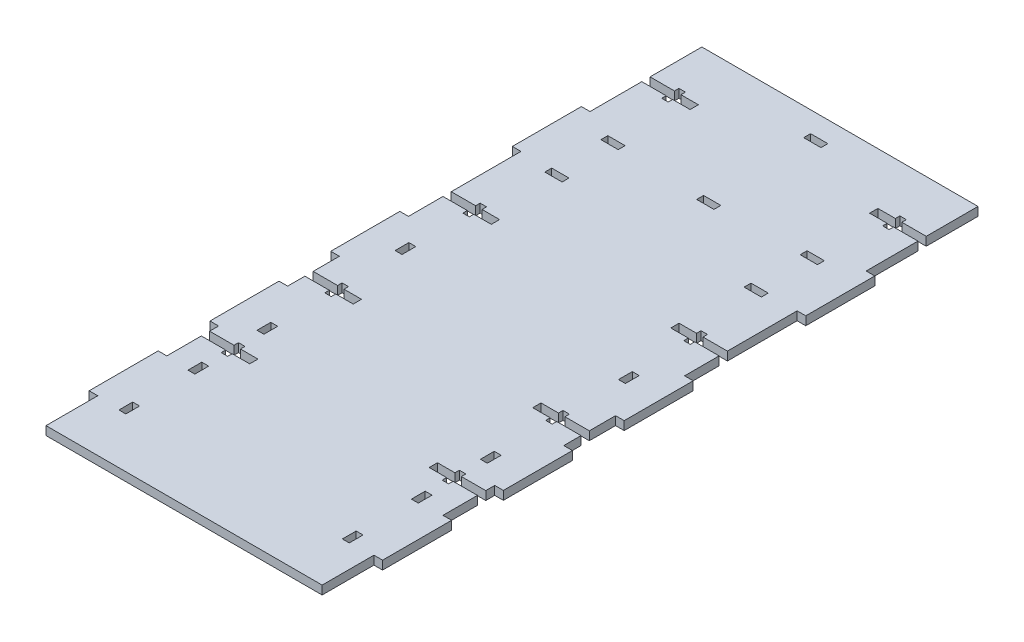
SolidWorks part; units mm, degrees
ref_plane "Front Plane" through (0, 0, 0) normal (0, 0, 1) x (1, 0, 0)
ref_plane "Top Plane" through (0, 0, 0) normal (0, 1, 0) x (1, 0, 0)
ref_plane "Right Plane" through (0, 0, 0) normal (1, 0, 0) x (0, 0, -1)
sketch "Sketch1" plane through (0, 0, 0) normal (0, 1, 0) x (1, 0, 0)
  line L1 (0, 0) -> (101.6, 0)
  line L2 (0, 0) -> (0, 241.3)
  line L3 (0, 241.3) -> (101.6, 241.3)
  line L4 (101.6, 0) -> (101.6, 241.3)
  dimension "D1" = 101.6
  dimension "D2" = 241.3
extrude "Boss-Extrude1" add sketch "Sketch1" along normal blind 3.175
sketch "Sketch2" plane through (0, 3.175, 0) normal (0, 1, 0) x (1, 0, 0)
  line L0 (50.8, 241.3) -> (50.8, 0) construction
  line L1 (8.4285, 23.4802) -> (10.9685, 23.4802)
  line L2 (8.4285, 23.4802) -> (8.4285, 18.4002)
  line L3 (8.4285, 18.4002) -> (10.9685, 18.4002)
  line L4 (10.9685, 23.4802) -> (10.9685, 18.4002)
  line L5 (101.6, 241.3) -> (0, 241.3) construction
  line L6 (0, 0) -> (101.6, 0) construction
  line L7 (8.4285, 48.8802) -> (8.4285, 43.8002)
  line L8 (19.05, 88.9) -> (82.55, 88.9)
  line L9 (19.05, 88.9) -> (19.05, 0)
  line L10 (19.05, 0) -> (82.55, 0)
  line L11 (82.55, 88.9) -> (82.55, 0)
  line L12 (19.05, 88.9) -> (82.55, 0) construction
  line L13 (19.05, 0) -> (82.55, 88.9) construction
  line L14 (8.4285, 48.8802) -> (10.9685, 48.8802)
  line L15 (10.9685, 48.8802) -> (10.9685, 43.8002)
  line L16 (8.4285, 43.8002) -> (10.9685, 43.8002)
  line L17 (8.4285, 74.2802) -> (8.4285, 69.2002)
  line L18 (8.4285, 74.2802) -> (10.9685, 74.2802)
  line L19 (10.9685, 74.2802) -> (10.9685, 69.2002)
  line L20 (8.4285, 69.2002) -> (10.9685, 69.2002)
  line L21 (0, 177.8) -> (0, 190.5)
  line L22 (19.05, 165.1) -> (82.55, 165.1)
  line L23 (19.05, 165.1) -> (19.05, 101.6)
  line L24 (19.05, 101.6) -> (82.55, 101.6)
  line L25 (82.55, 165.1) -> (82.55, 101.6)
  line L26 (19.05, 165.1) -> (82.55, 101.6) construction
  line L27 (19.05, 101.6) -> (82.55, 165.1) construction
  line L28 (0, 177.8) -> (28.575, 177.8)
  line L29 (0, 190.5) -> (28.575, 190.5)
  line L30 (28.575, 177.8) -> (28.575, 190.5)
  line L31 (0, 241.3) -> (0, 0) construction
  line L32 (8.4285, 125.0802) -> (8.4285, 120.0002)
  line L33 (22.225, 228.6) -> (79.375, 228.6)
  line L34 (22.225, 228.6) -> (22.225, 196.85)
  line L35 (22.225, 196.85) -> (79.375, 196.85)
  line L36 (79.375, 228.6) -> (79.375, 196.85)
  line L37 (22.225, 228.6) -> (79.375, 196.85) construction
  line L38 (22.225, 196.85) -> (79.375, 228.6) construction
  line L39 (8.4285, 125.0802) -> (10.9685, 125.0802)
  line L40 (10.9685, 125.0802) -> (10.9685, 120.0002)
  line L41 (8.4285, 120.0002) -> (10.9685, 120.0002)
  line L42 (0, 184.15) -> (28.575, 184.15) construction
  line L43 (10.9685, 175.0986) -> (17.3185, 175.0986)
  line L44 (10.9685, 175.0986) -> (10.9685, 172.5586)
  line L45 (10.9685, 172.5586) -> (17.3185, 172.5586)
  line L46 (17.3185, 175.0986) -> (17.3185, 172.5586)
  line L47 (10.9685, 195.7414) -> (17.3185, 195.7414)
  line L48 (17.3185, 193.2014) -> (17.3185, 195.7414)
  line L49 (10.9685, 193.2014) -> (17.3185, 193.2014)
  line L50 (10.9685, 193.2014) -> (10.9685, 195.7414)
  line L51 (22.225, 212.725) -> (79.375, 212.725) construction
  line L52 (47.625, 194.31) -> (53.975, 194.31)
  line L53 (47.625, 194.31) -> (47.625, 191.77)
  line L54 (47.625, 191.77) -> (53.975, 191.77)
  line L55 (53.975, 194.31) -> (53.975, 191.77)
  line L56 (47.625, 194.31) -> (53.975, 191.77) construction
  line L57 (47.625, 191.77) -> (53.975, 194.31) construction
  line L58 (47.625, 233.68) -> (53.975, 233.68)
  line L59 (53.975, 231.14) -> (53.975, 233.68)
  line L60 (47.625, 231.14) -> (53.975, 231.14)
  line L61 (47.625, 231.14) -> (47.625, 233.68)
  line L62 (17.78, 220.726) -> (0, 220.726) construction
  line L63 (0, 60.198) -> (8.9694, 60.198)
  line L64 (0, 60.198) -> (0, 57.15)
  line L65 (0, 57.15) -> (8.9694, 57.15)
  line L66 (17.78, 60.198) -> (17.78, 57.15)
  line L71 (0, 98.298) -> (8.9694, 98.298)
  line L72 (0, 98.298) -> (0, 95.25)
  line L73 (0, 95.25) -> (8.9694, 95.25)
  line L74 (17.78, 98.298) -> (17.78, 95.25)
  line L75 (0, 149.098) -> (8.9694, 149.098)
  line L76 (0, 149.098) -> (0, 146.05)
  line L77 (0, 146.05) -> (8.9694, 146.05)
  line L78 (17.78, 149.098) -> (17.78, 146.05)
  line L79 (0, 222.25) -> (8.9694, 222.25)
  line L80 (0, 222.25) -> (0, 219.202)
  line L81 (0, 219.202) -> (8.9694, 219.202)
  line L82 (17.78, 222.25) -> (17.78, 219.202)
  line L83 (8.9694, 217.551) -> (11.3506, 217.551)
  line L84 (8.9694, 217.551) -> (8.9694, 219.202)
  line L85 (8.9694, 223.901) -> (11.3506, 223.901)
  line L86 (11.3506, 217.551) -> (11.3506, 219.202)
  line L87 (8.9694, 217.551) -> (11.3506, 223.901) construction
  line L88 (8.9694, 223.901) -> (11.3506, 217.551) construction
  line L89 (8.9694, 222.25) -> (8.9694, 223.901)
  line L90 (11.3506, 222.25) -> (11.3506, 223.901)
  line L91 (9.5885, 222.25) -> (10.7315, 222.25)
  line L92 (11.3506, 222.25) -> (17.78, 222.25)
  line L93 (11.3506, 219.202) -> (17.78, 219.202)
  line L94 (0, 147.574) -> (17.78, 147.574) construction
  line L95 (0, 96.774) -> (17.78, 96.774) construction
  line L96 (8.9694, 144.399) -> (11.3506, 144.399)
  line L97 (8.9694, 144.399) -> (8.9694, 146.05)
  line L98 (8.9694, 150.749) -> (11.3506, 150.749)
  line L99 (11.3506, 144.399) -> (11.3506, 146.05)
  line L100 (8.9694, 144.399) -> (11.3506, 150.749) construction
  line L101 (8.9694, 150.749) -> (11.3506, 144.399) construction
  line L102 (0, 58.674) -> (17.78, 58.674) construction
  line L103 (8.9694, 93.599) -> (11.3506, 93.599)
  line L104 (8.9694, 93.599) -> (8.9694, 95.25)
  line L105 (8.9694, 99.949) -> (11.3506, 99.949)
  line L106 (11.3506, 93.599) -> (11.3506, 95.25)
  line L107 (8.9694, 93.599) -> (11.3506, 99.949) construction
  line L108 (8.9694, 99.949) -> (11.3506, 93.599) construction
  line L109 (11.3506, 98.298) -> (17.78, 98.298)
  line L110 (8.9694, 55.499) -> (11.3506, 55.499)
  line L111 (8.9694, 55.499) -> (8.9694, 57.15)
  line L112 (8.9694, 61.849) -> (11.3506, 61.849)
  line L113 (11.3506, 55.499) -> (11.3506, 57.15)
  line L114 (8.9694, 55.499) -> (11.3506, 61.849) construction
  line L115 (8.9694, 61.849) -> (11.3506, 55.499) construction
  line L116 (8.9694, 98.298) -> (8.9694, 99.949)
  line L117 (11.3506, 95.25) -> (17.78, 95.25)
  line L118 (11.3506, 98.298) -> (11.3506, 99.949)
  line L119 (11.3506, 57.15) -> (17.78, 57.15)
  line L120 (11.3506, 60.198) -> (11.3506, 61.849)
  line L121 (11.3506, 60.198) -> (17.78, 60.198)
  line L122 (8.9694, 60.198) -> (8.9694, 61.849)
  line L123 (8.9694, 149.098) -> (8.9694, 150.749)
  line L124 (11.3506, 149.098) -> (17.78, 149.098)
  line L125 (11.3506, 149.098) -> (11.3506, 150.749)
  line L126 (11.3506, 146.05) -> (17.78, 146.05)
  line L127 (93.1715, 18.4002) -> (90.6315, 18.4002)
  line L128 (90.6315, 23.4802) -> (90.6315, 18.4002)
  line L129 (93.1715, 23.4802) -> (90.6315, 23.4802)
  line L130 (93.1715, 23.4802) -> (93.1715, 18.4002)
  line L131 (90.2494, 60.198) -> (90.2494, 61.849)
  line L132 (92.6306, 61.849) -> (90.2494, 61.849)
  line L133 (92.6306, 60.198) -> (92.6306, 61.849)
  line L134 (101.6, 60.198) -> (92.6306, 60.198)
  line L135 (101.6, 60.198) -> (101.6, 57.15)
  line L136 (101.6, 57.15) -> (92.6306, 57.15)
  line L137 (92.6306, 55.499) -> (92.6306, 57.15)
  line L138 (92.6306, 55.499) -> (90.2494, 55.499)
  line L139 (90.2494, 55.499) -> (90.2494, 57.15)
  line L140 (90.2494, 57.15) -> (83.82, 57.15)
  line L141 (83.82, 60.198) -> (83.82, 57.15)
  line L142 (90.2494, 60.198) -> (83.82, 60.198)
  line L143 (93.1715, 48.8802) -> (90.6315, 48.8802)
  line L144 (90.6315, 48.8802) -> (90.6315, 43.8002)
  line L145 (93.1715, 43.8002) -> (90.6315, 43.8002)
  line L146 (93.1715, 48.8802) -> (93.1715, 43.8002)
  line L147 (93.1715, 74.2802) -> (90.6315, 74.2802)
  line L148 (90.6315, 74.2802) -> (90.6315, 69.2002)
  line L149 (93.1715, 69.2002) -> (90.6315, 69.2002)
  line L150 (93.1715, 74.2802) -> (93.1715, 69.2002)
  line L151 (92.6306, 93.599) -> (92.6306, 95.25)
  line L152 (101.6, 95.25) -> (92.6306, 95.25)
  line L153 (101.6, 98.298) -> (101.6, 95.25)
  line L154 (101.6, 98.298) -> (92.6306, 98.298)
  line L155 (92.6306, 98.298) -> (92.6306, 99.949)
  line L156 (92.6306, 99.949) -> (90.2494, 99.949)
  line L157 (90.2494, 98.298) -> (90.2494, 99.949)
  line L158 (90.2494, 98.298) -> (83.82, 98.298)
  line L159 (83.82, 98.298) -> (83.82, 95.25)
  line L160 (90.2494, 95.25) -> (83.82, 95.25)
  line L161 (90.2494, 93.599) -> (90.2494, 95.25)
  line L162 (92.6306, 93.599) -> (90.2494, 93.599)
  line L163 (93.1715, 125.0802) -> (90.6315, 125.0802)
  line L164 (90.6315, 125.0802) -> (90.6315, 120.0002)
  line L165 (93.1715, 120.0002) -> (90.6315, 120.0002)
  line L166 (93.1715, 125.0802) -> (93.1715, 120.0002)
  line L167 (92.6306, 144.399) -> (92.6306, 146.05)
  line L168 (101.6, 146.05) -> (92.6306, 146.05)
  line L169 (101.6, 149.098) -> (101.6, 146.05)
  line L170 (101.6, 149.098) -> (92.6306, 149.098)
  line L171 (92.6306, 149.098) -> (92.6306, 150.749)
  line L172 (92.6306, 150.749) -> (90.2494, 150.749)
  line L173 (90.2494, 149.098) -> (90.2494, 150.749)
  line L174 (90.2494, 149.098) -> (83.82, 149.098)
  line L175 (83.82, 149.098) -> (83.82, 146.05)
  line L176 (90.2494, 146.05) -> (83.82, 146.05)
  line L177 (90.2494, 144.399) -> (90.2494, 146.05)
  line L178 (92.6306, 144.399) -> (90.2494, 144.399)
  line L179 (90.2494, 217.551) -> (90.2494, 219.202)
  line L180 (92.6306, 217.551) -> (90.2494, 217.551)
  line L181 (92.6306, 217.551) -> (92.6306, 219.202)
  line L182 (101.6, 219.202) -> (92.6306, 219.202)
  line L183 (101.6, 222.25) -> (101.6, 219.202)
  line L184 (101.6, 222.25) -> (92.6306, 222.25)
  line L185 (92.6306, 222.25) -> (92.6306, 223.901)
  line L186 (92.6306, 223.901) -> (90.2494, 223.901)
  line L187 (90.2494, 222.25) -> (90.2494, 223.901)
  line L188 (90.2494, 222.25) -> (83.82, 222.25)
  line L189 (83.82, 222.25) -> (83.82, 219.202)
  line L190 (90.2494, 219.202) -> (83.82, 219.202)
  line L191 (90.6315, 193.2014) -> (90.6315, 195.7414)
  line L192 (90.6315, 193.2014) -> (84.2815, 193.2014)
  line L193 (84.2815, 193.2014) -> (84.2815, 195.7414)
  line L194 (90.6315, 195.7414) -> (84.2815, 195.7414)
  line L195 (90.6315, 172.5586) -> (84.2815, 172.5586)
  line L196 (84.2815, 175.0986) -> (84.2815, 172.5586)
  line L197 (90.6315, 175.0986) -> (84.2815, 175.0986)
  line L198 (90.6315, 175.0986) -> (90.6315, 172.5586)
  point P10 (50.8, 44.45)
  point P15 (50.8, 133.35)
  point P34 (50.8, 212.725)
  point P53 (50.8, 193.04)
  point P64 (10.16, 220.726)
  point P87 (10.16, 147.574)
  point P102 (10.16, 96.774)
  point P109 (10.16, 58.674)
  dimension "D1" = 5.08
  dimension "D2" = 2.54
  dimension "D3" = 88.9
  dimension "D4" = 63.5
  dimension "D6" = 63.5
  dimension "D7" = 12.7
  dimension "D8" = 28.575
  dimension "D9" = 12.7
  dimension "D10" = 12.7
  dimension "D11" = 31.75
  dimension "D12" = 6.35
  dimension "D13" = 57.15
  dimension "D15" = 6.35
  dimension "D16" = 2.54
  dimension "D17" = 6.35
  dimension "D18" = 2.54
  dimension "D19" = 2.54
  dimension "D20" = 17.78
  dimension "D21" = 17.78
  dimension "D22" = 17.78
  dimension "D23" = 17.78
  dimension "D24" = 3.048
  dimension "D25" = 3.048
  dimension "D26" = 3.048
  dimension "D27" = 3.048
  dimension "D28" = 19.05
  dimension "D29" = 57.15
  dimension "D30" = 95.25
  dimension "D31" = 146.05
  dimension "D32" = 2.3813
  dimension "D33" = 6.35
  dimension "D34" = 7.62
  dimension "D35" = 2.3812
  dimension "D36" = 6.35
  dimension "D37" = 7.62
  dimension "D38" = 2.3813
  dimension "D39" = 6.35
  dimension "D40" = 2.3812
  dimension "D41" = 6.35
  dimension "D5" = 3
  dimension "D14" = 2
extrude "Cut-Extrude1" cut sketch "Sketch2" against normal blind 6.35
sketch "Sketch3" plane through (0, 3.175, 0) normal (0, 1, 0) x (1, 0, 0)
  line L0 (0, 219.202) -> (0, 149.098) construction
  line L1 (-3.175, 200.152) -> (3.175, 200.152)
  line L2 (-3.175, 200.152) -> (-3.175, 174.752)
  line L3 (-3.175, 174.752) -> (3.175, 174.752)
  line L4 (3.175, 200.152) -> (3.175, 174.752)
  line L5 (-3.175, 200.152) -> (3.175, 174.752) construction
  line L6 (-3.175, 174.752) -> (3.175, 200.152) construction
  line L7 (0, 219.202) -> (8.9694, 219.202) construction
  line L8 (0, 146.05) -> (0, 98.298) construction
  line L9 (-3.175, 107.95) -> (3.175, 107.95)
  line L10 (-3.175, 107.95) -> (-3.175, 133.35)
  line L11 (-3.175, 133.35) -> (3.175, 133.35)
  line L12 (3.175, 107.95) -> (3.175, 133.35)
  line L13 (-3.175, 107.95) -> (3.175, 133.35) construction
  line L14 (-3.175, 133.35) -> (3.175, 107.95) construction
  line L15 (0, 146.05) -> (8.9694, 146.05) construction
  line L16 (0, 95.25) -> (0, 60.198) construction
  line L17 (-3.175, 63.5) -> (3.175, 63.5)
  line L18 (-3.175, 63.5) -> (-3.175, 88.9)
  line L19 (-3.175, 88.9) -> (3.175, 88.9)
  line L20 (3.175, 63.5) -> (3.175, 88.9)
  line L21 (-3.175, 63.5) -> (3.175, 88.9) construction
  line L22 (-3.175, 88.9) -> (3.175, 63.5) construction
  line L23 (0, 95.25) -> (8.9694, 95.25) construction
  line L24 (0, 57.15) -> (0, 0) construction
  line L25 (3.175, 44.45) -> (-3.175, 44.45)
  line L26 (3.175, 44.45) -> (3.175, 19.05)
  line L27 (3.175, 19.05) -> (-3.175, 19.05)
  line L28 (-3.175, 44.45) -> (-3.175, 19.05)
  line L29 (3.175, 44.45) -> (-3.175, 19.05) construction
  line L30 (3.175, 19.05) -> (-3.175, 44.45) construction
  line L31 (0, 0) -> (101.6, 0) construction
  line L32 (50.8, 241.3) -> (50.8, 0) construction
  line L33 (101.6, 241.3) -> (0, 241.3) construction
  line L34 (98.425, 19.05) -> (104.775, 19.05)
  line L35 (104.775, 44.45) -> (104.775, 19.05)
  line L36 (98.425, 44.45) -> (104.775, 44.45)
  line L37 (98.425, 44.45) -> (98.425, 19.05)
  line L38 (104.775, 88.9) -> (98.425, 88.9)
  line L39 (98.425, 63.5) -> (98.425, 88.9)
  line L40 (104.775, 63.5) -> (98.425, 63.5)
  line L41 (104.775, 63.5) -> (104.775, 88.9)
  line L42 (104.775, 133.35) -> (98.425, 133.35)
  line L43 (98.425, 107.95) -> (98.425, 133.35)
  line L44 (104.775, 107.95) -> (98.425, 107.95)
  line L45 (104.775, 107.95) -> (104.775, 133.35)
  line L46 (104.775, 174.752) -> (98.425, 174.752)
  line L47 (98.425, 200.152) -> (98.425, 174.752)
  line L48 (104.775, 200.152) -> (98.425, 200.152)
  line L49 (104.775, 200.152) -> (104.775, 174.752)
  point P0 (0, 187.452)
  point P9 (0, 120.65)
  point P18 (0, 76.2)
  point P27 (0, 31.75)
  dimension "D1" = 25.4
  dimension "D2" = 6.35
  dimension "D3" = 19.05
  dimension "D4" = 6.35
  dimension "D5" = 25.4
  dimension "D6" = 12.7
  dimension "D7" = 25.4
  dimension "D8" = 6.35
  dimension "D9" = 6.35
  dimension "D10" = 6.35
  dimension "D11" = 25.4
  dimension "D12" = 19.05
extrude "Boss-Extrude2" add sketch "Sketch3" against normal blind 3.175
